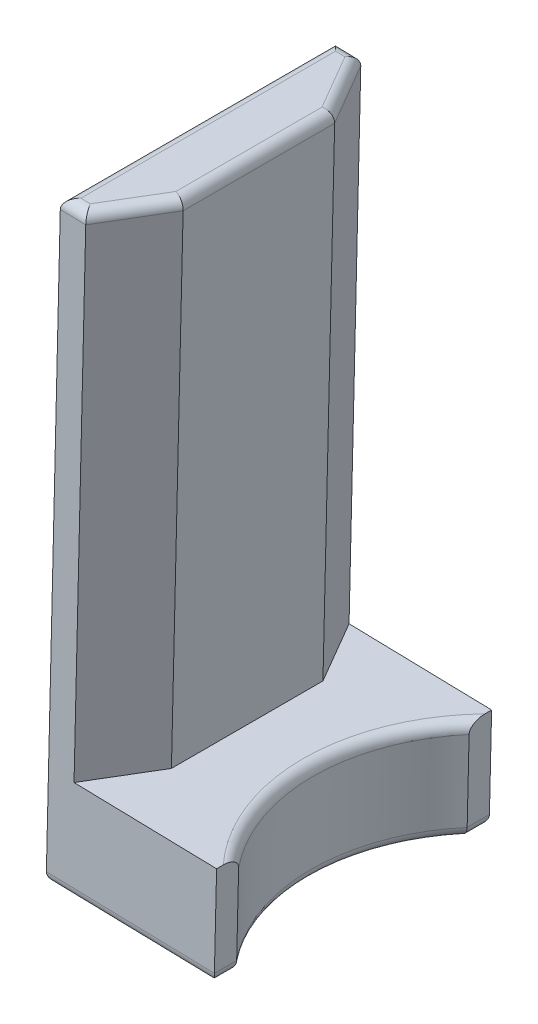
SolidWorks part; units mm, degrees
material "6061-T6 (SS)"
ref_plane "Front" through (0, 0, 0) normal (0, 0, 1) x (1, 0, 0)
ref_plane "Top" through (0, 0, 0) normal (0, 1, 0) x (1, 0, 0)
ref_plane "Right" through (0, 0, 0) normal (1, 0, 0) x (0, 0, -1)
sketch "Sketch1" plane through (0, 0, 0) normal (0, 0, 1) x (1, 0, 0)
  line L4 (0, 0) -> (0, 242.8932)
  line L5 (340.4001, 0) -> (353.2624, 536.8) construction
  line L6 (279.1618, 74.2828) -> (290.9941, 568.093)
  line L7 (290.9941, 568.093) -> (240.0087, 569.3146)
  line L8 (240.0087, 569.3146) -> (228.1765, 75.5045) construction
  line L9 (228.1765, 75.5045) -> (279.1618, 74.2828) construction
  line L10 (239.6933, 326.7526) -> (285.1852, 325.6626) construction
  line L11 (244.2699, 289.1803) -> (284.288, 288.2214) construction
  line L12 (340.4001, 0) -> (339.3876, -42.2576) construction
  line L13 (340.3833, -0.6998) -> (346.3816, -0.8435)
  line L14 (340.3833, -0.6998) -> (353.1186, 530.7962)
  line L15 (346.3816, -0.8435) -> (355.1165, 363.7004)
  line L17 (340.3833, -0.6998) -> (346.2618, -5.8435)
  line L18 (346.2618, -5.8435) -> (346.3816, -0.8435)
  line L19 (355.1165, 363.7004) -> (374.8608, 363.2273)
  line L20 (374.8608, 363.2273) -> (375.0764, 372.2247)
  line L21 (375.0764, 372.2247) -> (383.8239, 372.0151)
  line L22 (383.8239, 372.0151) -> (384.6384, 406.0054)
  line L23 (384.6384, 406.0054) -> (365.6438, 406.4605)
  line L24 (365.6438, 406.4605) -> (365.9073, 417.4573)
  line L25 (365.9073, 417.4573) -> (370.406, 417.3496)
  line L26 (370.406, 417.3496) -> (371.8672, 478.332)
  line L27 (371.8672, 478.332) -> (378.8652, 478.1644)
  line L28 (378.8652, 478.1644) -> (379.3443, 498.1586)
  line L29 (379.3443, 498.1586) -> (384.3429, 498.0389)
  line L30 (384.3429, 498.0389) -> (384.4794, 503.7372)
  line L31 (384.4794, 503.7372) -> (380.9804, 503.8211)
  line L32 (380.9804, 503.8211) -> (381.1864, 512.4186)
  line L33 (381.1864, 512.4186) -> (384.6854, 512.3348)
  line L34 (384.6854, 512.3348) -> (384.822, 518.0331)
  line L35 (384.822, 518.0331) -> (387.8211, 517.9613)
  line L36 (387.8211, 517.9613) -> (388.1085, 529.9578)
  line L37 (388.1085, 529.9578) -> (353.1186, 530.7962)
  line L38 (321.1262, 364.5149) -> (288.1356, 365.3053)
  line L39 (288.1356, 365.3053) -> (288.6147, 385.2996)
  line L40 (300.6113, 385.0122) -> (321.6052, 384.5091)
  line L41 (321.6052, 384.5091) -> (321.1262, 364.5149)
  line L42 (288.6147, 385.2996) -> (290.9622, 483.2715)
  line L43 (290.9622, 483.2715) -> (302.9588, 482.984)
  line L44 (302.9588, 482.984) -> (300.6113, 385.0122)
  circle A0 centre (244.2699, 289.1803) radius 4
  circle A1 centre (239.6933, 326.7526) radius 4
  circle A2 centre (340.4001, 0) radius 5.3016 construction
  dimension "D5" = 8
  dimension "D7" = 289.1803
  dimension "D1" = 244.2699
  dimension "D2" = 239.6933
  dimension "D3" = 25.75
  dimension "D4" = 326.7526
  dimension "D6" = 340.4001
  dimension "D8" = 9
  dimension "D9" = 242.5
  dimension "D10" = 51
  dimension "D11" = 214
  dimension "D12" = 0.7
  dimension "D13" = 6
  dimension "D14" = 5
  dimension "D15" = 369.65
  dimension "D16" = 34.5
  dimension "D17" = 34
  dimension "D18" = 15.5
  dimension "D19" = 11
  dimension "D20" = 20
  dimension "D21" = 61
  dimension "D22" = 27
  dimension "D23" = 20
  dimension "D24" = 32
  dimension "D25" = 5.7
  dimension "D26" = 28.5
  dimension "D27" = 32
  dimension "D28" = 5.7
  dimension "D29" = 20
  dimension "D30" = 35
  dimension "D31" = 12
  dimension "D32" = 2
  dimension "D33" = 20
  dimension "D34" = 35
  dimension "D35" = 98
  dimension "D36" = 12
extrude "Boss-Extrude1" add sketch "Sketch1" against normal mid plane 54 contours L44 L43 L42 L39 L38 L41 L40
sketch "Sketch2" plane through (8.9134, 371.9958, 0) normal (-0.024, -0.9997, 0) x (0.9997, -0.024, 0)
  line L0 (279.3023, -27) -> (279.3023, 27) construction
  circle A0 centre (340.3023, 0) radius 36
  dimension "D1" = 72
  dimension "D2" = 61
extrude "Cut-Extrude1" cut sketch "Sketch2" against normal blind 54
chamfer "Chamfer1" distance 7 angle 60 1 edges at (301.785, 433.9981, 27)
chamfer "Chamfer2" distance 7 angle 60 1 edges at (301.785, 433.9981, -27)
fillet "Fillet1" radius 2 13 edges at (304.6309, 364.9101, -27) (288.1356, 365.3053, 0) (304.6309, 364.9101, 27) (321.1262, 364.5149, 24.8137) (313.1285, 364.7065, 0) (321.1262, 364.5149, -24.8137) (299.4598, 483.0679, 20.9378) (293.4615, 483.2116, 27) (290.9622, 483.2715, 0) (293.4615, 483.2116, -27) (299.4598, 483.0679, -20.9378) (302.9588, 482.984, 0) (313.6075, 384.7007, 0)
